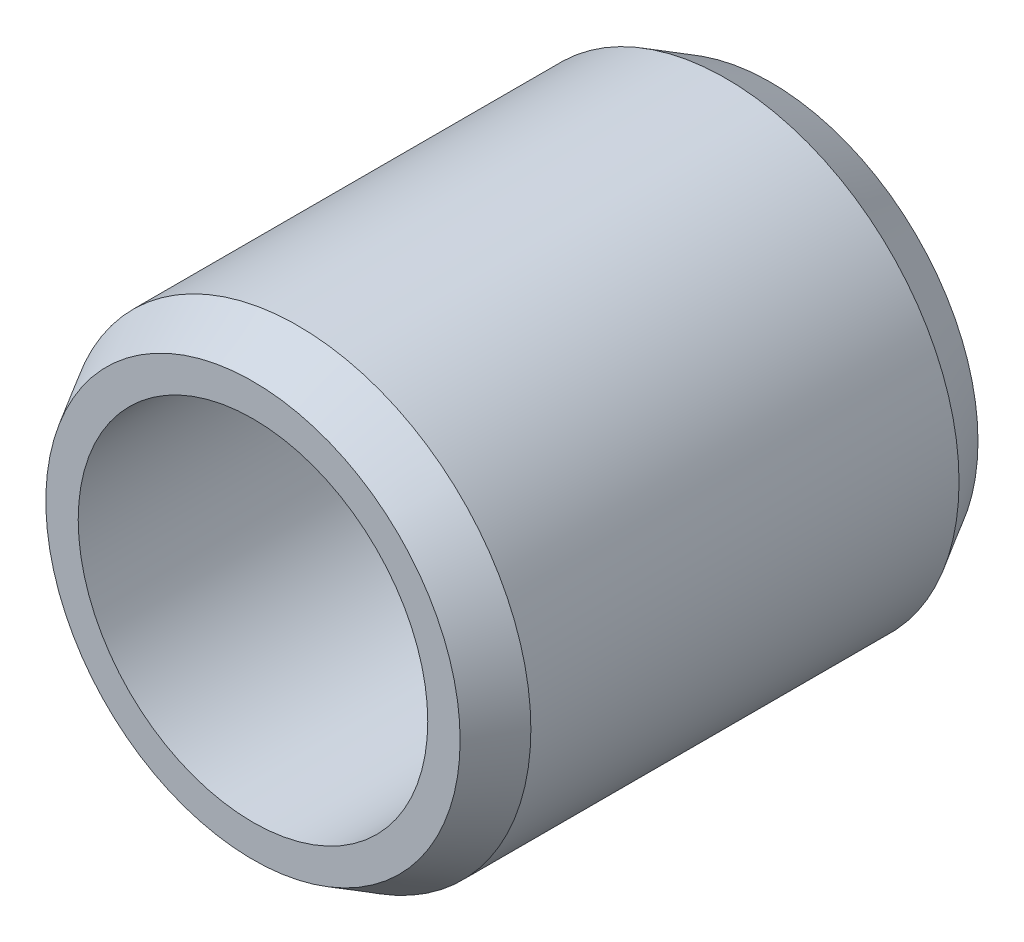
SolidWorks part; units mm, degrees
material "ABS"
ref_plane "Front Plane" through (0, 0, 0) normal (0, 0, 1) x (1, 0, 0)
ref_plane "Top Plane" through (0, 0, 0) normal (0, 1, 0) x (1, 0, 0)
ref_plane "Right Plane" through (0, 0, 0) normal (1, 0, 0) x (0, 0, -1)
sketch "Sketch1" plane through (0, 0, 0) normal (0, 0, 1) x (1, 0, 0)
  circle A0 centre (0, 0) radius 4.5
  circle A1 centre (0, 0) radius 3.375
  dimension "D1" = 6.75
  dimension "D2" = 9
extrude "Boss-Extrude1" add sketch "Sketch1" along normal blind 10
chamfer "Chamfer1" distance 0.5 angle 60 2 edges at (4.5, 0, 10) (4.5, 0, 0)
